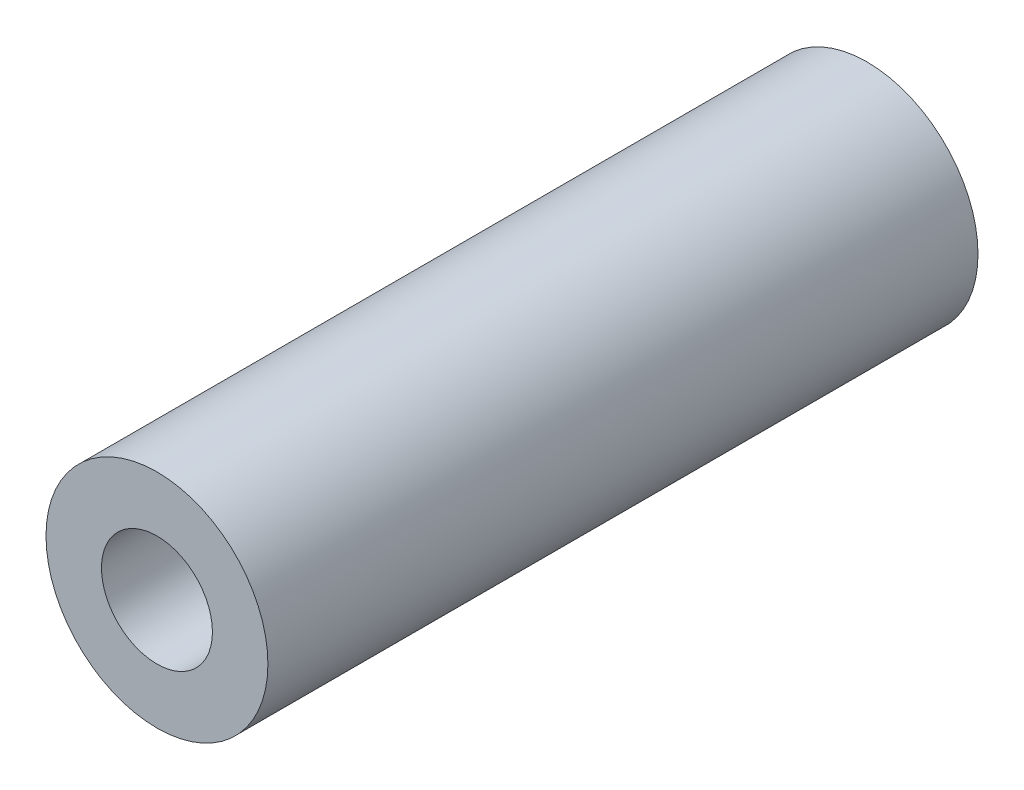
SolidWorks part; units mm, degrees
material "6061 合金"
ref_plane "前视基准面" through (0, 0, 0) normal (0, 0, 1) x (1, 0, 0)
ref_plane "上视基准面" through (0, 0, 0) normal (0, 1, 0) x (1, 0, 0)
ref_plane "右视基准面" through (0, 0, 0) normal (1, 0, 0) x (0, 0, -1)
sketch "草图1" plane through (0, 0, 0) normal (0, 0, 1) x (1, 0, 0)
  circle A1 centre (0, 0) radius 2.5
  dimension "D1" = 5
extrude "凸台-拉伸1" add sketch "草图1" along normal blind 16
hole_wizard "M3 螺纹孔1" positions "草图2" profile "草图3" tap size "M3" standard "GB" end condition through all
sketch "草图2" plane through (0, 0, 16) normal (0, 0, 1) x (1, 0, 0)
  point P0 (0, 0)
sketch "草图3" plane through (0, 0, 16) normal (1, 0, 0) x (0, -1, 0)
  line L0 (0, 0) -> (0, 16)
  line L1 (0, 16) -> (1.25, 16)
  line L2 (1.25, 16) -> (1.25, 0)
  line L5 (1.25, 0) -> (0, 0)
  line L11 (0, -6.35) -> (0, 107.95) construction
  dimension "通孔螺纹孔钻头直径" = 2.5
  dimension "通孔螺纹孔钻头深度" = 16
cosmetic thread "孔螺蚊线1" parameters "D2"=3
